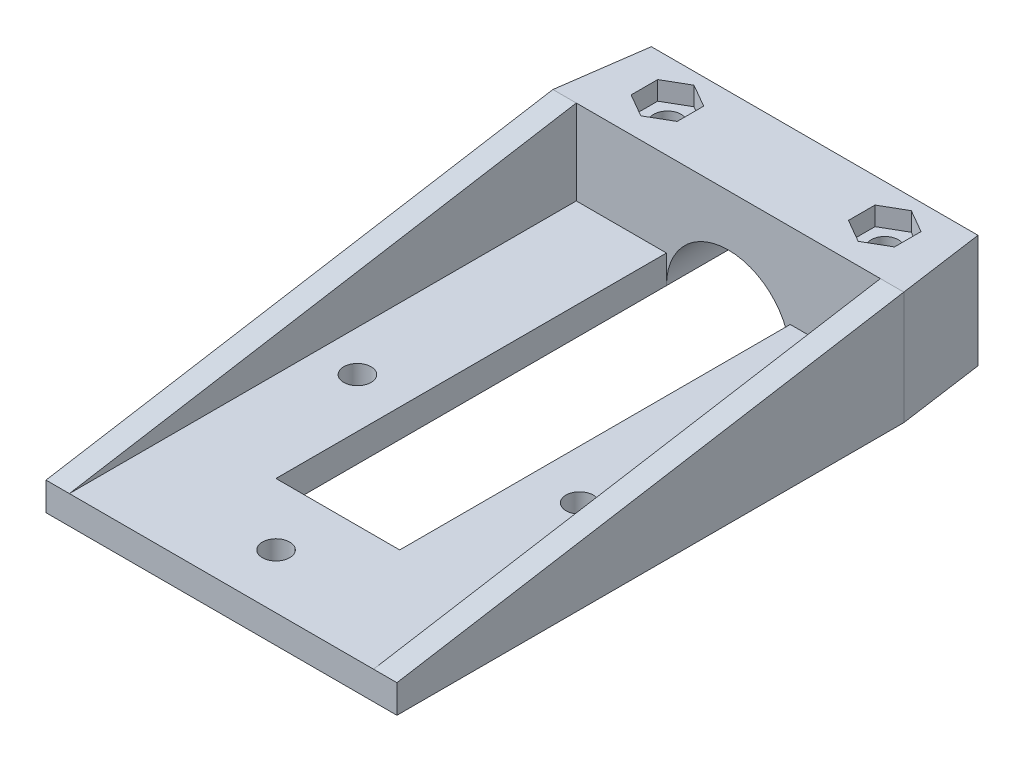
SolidWorks part; units mm, degrees
ref_plane "Front Plane" through (0, 0, 0) normal (0, 0, 1) x (1, 0, 0)
ref_plane "Top Plane" through (0, 0, 0) normal (0, 1, 0) x (1, 0, 0)
ref_plane "Right Plane" through (0, 0, 0) normal (1, 0, 0) x (0, 0, -1)
sketch "Sketch6" plane through (0, 0, 0) normal (0, 1, 0) x (1, 0, 0)
  line L0 (-16.8369, 5.7834) -> (13.1631, 5.7834)
  line L1 (13.1631, 5.7834) -> (20.6631, -47.5819)
  line L2 (20.6631, -47.5819) -> (-24.3369, -47.5819)
  line L3 (-24.3369, -47.5819) -> (-16.8369, 5.7834)
  circle A0 centre (13.1631, -5.2166) radius 1.78
  circle A1 centre (-16.8369, -5.2166) radius 1.78
  circle A2 centre (-26.4869, -43.0491) radius 1.78
  circle A3 centre (22.8131, -43.0491) radius 1.78
  dimension "D3" = 98
  dimension "D4" = 3.56
  dimension "D5" = 3.56
  dimension "D2" = 45
  dimension "D6" = 30
  dimension "D7" = 11
  dimension "D8" = 11
  dimension "D9" = 98
  dimension "D10" = 82
  dimension "D11" = 82
  dimension "D12" = 30
extrude "Boss-Extrude3" add sketch "Sketch6" along normal blind 14.5 contours L3 L0 L1 L2
sketch "Sketch8" plane through (0, 0, 47.5819) normal (0, 0, 1) x (1, 0, 0)
  line L0 (20.6631, 0) -> (-24.3369, 0) construction
  circle A0 centre (-1.8369, 0) radius 7.935
  dimension "D1" = 15.87
extrude "Cut-Extrude3" cut sketch "Sketch8" against normal blind 88
sketch "Sketch18" plane through (0, 14.5, 0) normal (0, 1, 0) x (1, 0, 0)
  line L0 (20.6631, -47.5819) -> (-24.3369, -47.5819) construction
  line L1 (-24.3369, -47.5819) -> (-16.8369, 5.7834) construction
  line L2 (13.1631, 5.7834) -> (20.6631, -47.5819) construction
  line L10 (-15.7718, -44.8683) -> (-12.8218, -43.1651)
  line L11 (-12.8218, -43.1651) -> (-12.8218, -39.7587)
  line L12 (-12.8218, -39.7587) -> (-15.7718, -38.0556)
  line L13 (-15.7718, -38.0556) -> (-18.7218, -39.7587)
  line L14 (-18.7218, -39.7587) -> (-18.7218, -43.1651)
  line L15 (-18.7218, -43.1651) -> (-15.7718, -44.8683)
  line L16 (12.098, -44.8683) -> (15.048, -43.1651)
  line L17 (15.048, -43.1651) -> (15.048, -39.7587)
  line L18 (15.048, -39.7587) -> (12.098, -38.0556)
  line L19 (12.098, -38.0556) -> (9.148, -39.7587)
  line L20 (9.148, -39.7587) -> (9.148, -43.1651)
  line L21 (9.148, -43.1651) -> (12.098, -44.8683)
  line L22 (11.3893, -26.016) -> (14.3893, -24.284)
  line L23 (14.3893, -24.284) -> (14.3893, -20.8199)
  line L24 (14.3893, -20.8199) -> (11.3893, -19.0878)
  line L25 (11.3893, -19.0878) -> (8.3893, -20.8199)
  line L26 (8.3893, -20.8199) -> (8.3893, -24.284)
  line L27 (8.3893, -24.284) -> (11.3893, -26.016)
  line L28 (-15.0632, -26.016) -> (-12.0632, -24.284)
  line L29 (-12.0632, -24.284) -> (-12.0632, -20.8199)
  line L30 (-12.0632, -20.8199) -> (-15.0632, -19.0878)
  line L31 (-15.0632, -19.0878) -> (-18.0632, -20.8199)
  line L32 (-18.0632, -20.8199) -> (-18.0632, -24.284)
  line L33 (-18.0632, -24.284) -> (-15.0632, -26.016)
  circle A0 centre (-15.0632, -22.5519) radius 3 construction
  circle A1 centre (-15.7718, -41.4619) radius 2.95 construction
  circle A2 centre (12.098, -41.4619) radius 2.95 construction
  circle A3 centre (11.3893, -22.5519) radius 3 construction
  point P0 (-15.7718, -41.4619)
  point P1 (-15.0632, -22.5519)
  point P2 (12.098, -41.4619)
  point P3 (11.3893, -22.5519)
  dimension "D1" = 6.12
  dimension "D2" = 7.63
  dimension "D3" = 25.03
  dimension "D4" = 5.7
  dimension "D5" = 6.12
  dimension "D6" = 7.63
  dimension "D7" = 25.03
  dimension "D8" = 5.7
  dimension "D9" = 6
  dimension "D10" = 5.9
  dimension "D11" = 5.9
  dimension "D12" = 6
sketch "Sketch19" plane through (0, 0, 0) normal (0, -1, 0) x (1, 0, 0)
  line L1 (-20.0152, 40.7177) -> (-17.249, 37.4149)
  line L2 (-17.249, 37.4149) -> (-13.0056, 38.1592)
  line L3 (-13.0056, 38.1592) -> (-11.5284, 42.2062)
  line L4 (-11.5284, 42.2062) -> (-14.2947, 45.5089)
  line L5 (-14.2947, 45.5089) -> (-18.5381, 44.7647)
  line L6 (-18.5381, 44.7647) -> (-20.0152, 40.7177)
  line L7 (-16.9187, 22.0232) -> (-15.5331, 20.6806)
  line L8 (-15.5331, 20.6806) -> (-13.6775, 21.2093)
  line L9 (-13.6775, 21.2093) -> (-13.2076, 23.0806)
  line L10 (-13.2076, 23.0806) -> (-14.5932, 24.4232)
  line L11 (-14.5932, 24.4232) -> (-16.4488, 23.8945)
  line L12 (-16.4488, 23.8945) -> (-16.9187, 22.0232)
  line L13 (16.8606, 20.993) -> (15.475, 26.5108)
  line L14 (15.475, 26.5108) -> (10.0037, 28.0696)
  line L15 (10.0037, 28.0696) -> (5.918, 24.1108)
  line L16 (5.918, 24.1108) -> (7.3037, 18.5931)
  line L17 (7.3037, 18.5931) -> (12.775, 17.0342)
  line L18 (12.775, 17.0342) -> (16.8606, 20.993)
  line L19 (20.0445, 40.0682) -> (17.2783, 47.6469)
  line L20 (17.2783, 47.6469) -> (9.3318, 49.0407)
  line L21 (9.3318, 49.0407) -> (4.1515, 42.8557)
  line L22 (4.1515, 42.8557) -> (6.9177, 35.2769)
  line L23 (6.9177, 35.2769) -> (14.8642, 33.8832)
  line L24 (14.8642, 33.8832) -> (20.0445, 40.0682)
  circle A0 centre (-15.7718, 41.4619) radius 3.731 construction
  circle A1 centre (-15.0632, 22.5519) radius 1.6709 construction
  circle A2 centre (11.3893, 22.5519) radius 4.9269 construction
  circle A3 centre (12.098, 41.4619) radius 6.9869 construction
  point P0 (-15.7718, 41.4619)
  point P1 (-15.0632, 22.5519)
  point P3 (11.3893, 22.5519)
  point P5 (12.098, 41.4619)
extrude "Cut-Extrude9" cut sketch "Sketch18" against normal blind 2.4
hole_wizard "#39 (0.13779528) Diameter Hole1" positions "3DSketch1" profile "Sketch21" hole size "#39" standard "ANSI Inch" end condition through all
sketch3d "3DSketch1"
  point P0 (-15.0632, 14.5, 22.5519)
  point P3 (11.3893, 14.5, 22.5519)
  point P6 (-15.7718, 14.5, 41.4619)
  point P9 (12.098, 14.5, 41.4619)
sketch "Sketch21" plane through (-15.0632, 14.5, 22.5519) normal (1, 0, 0) x (0, 0, 1)
  line L0 (0, 0) -> (0, 14.5)
  line L1 (0, 14.5) -> (1.75, 14.5)
  line L2 (1.75, 14.5) -> (1.75, 0)
  line L5 (1.75, 0) -> (0, 0)
  line L11 (0, -6.35) -> (0, 107.95) construction
  dimension "Thru Hole Dia." = 3.5
  dimension "Thru Hole Depth" = 14.5
sketch "Sketch22" plane through (0, 14.5, 0) normal (0, 1, 0) x (1, 0, 0)
  line L0 (-22.7813, -36.5132) -> (19.1075, -36.5132)
  line L1 (-24.3369, -47.5819) -> (-16.8369, 5.7834) construction
  line L2 (13.1631, 5.7834) -> (20.6631, -47.5819) construction
  line L3 (19.1075, -36.5132) -> (13.1631, 5.7834)
  line L4 (13.1631, 5.7834) -> (-16.8369, 5.7834)
  line L5 (-16.8369, 5.7834) -> (-22.7813, -36.5132)
extrude "Cut-Extrude10" cut sketch "Sketch22" against normal blind 22.4
sketch "Sketch23" plane through (0, 0, 47.5819) normal (0, 0, 1) x (1, 0, 0)
  line L0 (-24.3369, 0) -> (-24.3369, 3.625)
  line L1 (-24.3369, 14.5) -> (-24.3369, 0) construction
  line L2 (-24.3369, 3.625) -> (-8.8955, 3.625)
  line L3 (20.6631, 0) -> (20.6631, 3.625)
  line L4 (20.6631, 14.5) -> (20.6631, 0) construction
  line L5 (20.6631, 3.625) -> (5.2217, 3.625)
  line L6 (-24.3369, 0) -> (-9.7719, 0)
  line L7 (20.6631, 0) -> (6.0981, 0) construction
  arc A0 (6.0981, 0) -> (-9.7719, 0) centre (-1.8369, 0) ccw construction
  spline S0 degree 2 poles (-9.7719, 0) (-9.7646, 1.9214) (-8.8955, 3.625) knots 0 0 0 1 1 1
  spline S1 degree 2 poles (6.0981, 0) (6.0907, 1.9214) (5.2217, 3.625) knots 0 0 0 1 1 1
  dimension "D1" = 3.625
  dimension "D2" = 3.625
sketch "Sketch24" plane through (0, 0, 0) normal (0, -1, 0) x (1, 0, 0)
  line L1 (-15.7718, 38.0556) -> (-12.8218, 39.7587)
  line L2 (-12.8218, 39.7587) -> (-12.8218, 43.1651)
  line L3 (-12.8218, 43.1651) -> (-15.7718, 44.8683)
  line L4 (-15.7718, 44.8683) -> (-18.7218, 43.1651)
  line L5 (-18.7218, 43.1651) -> (-18.7218, 39.7587)
  line L6 (-18.7218, 39.7587) -> (-15.7718, 38.0556)
  line L7 (12.098, 38.0556) -> (15.048, 39.7587)
  line L8 (15.048, 39.7587) -> (15.048, 43.1651)
  line L9 (15.048, 43.1651) -> (12.098, 44.8683)
  line L10 (12.098, 44.8683) -> (9.148, 43.1651)
  line L11 (9.148, 43.1651) -> (9.148, 39.7587)
  line L12 (9.148, 39.7587) -> (12.098, 38.0556)
  circle A0 centre (-15.7718, 41.4619) radius 2.95 construction
  circle A1 centre (12.098, 41.4619) radius 2.95 construction
  point P0 (-15.7718, 41.4619)
  point P1 (12.098, 41.4619)
  dimension "D1" = 5.9
  dimension "D2" = 5.9
extrude "Cut-Extrude11" cut sketch "Sketch24" against normal blind 2.4
sketch "Sketch27" plane through (0, 0, 0) normal (0, 1, 0) x (1, 0, 0)
  line L0 (-9.7719, -47.2249) -> (-9.7719, -47.5819)
  line L1 (-9.7719, -47.5819) -> (-9.7719, -97.6619)
  line L2 (-9.7719, -112.5819) -> (-24.3369, -112.5819)
  line L3 (-24.3369, -112.5819) -> (-24.3369, -47.5819)
  line L4 (-9.7719, -97.6619) -> (6.0981, -97.6619)
  line L5 (6.0981, -47.5819) -> (6.0981, -97.6619)
  line L6 (20.6631, -47.5819) -> (20.6631, -112.5819)
  line L7 (20.6631, -112.5819) -> (-9.7719, -112.5819)
  line L9 (-24.3369, -47.5819) -> (-9.7719, -47.5819)
  line L10 (-24.3369, -47.5819) -> (-9.7719, -47.5819)
  line L11 (6.0981, -47.5819) -> (20.6631, -47.5819)
  dimension "D1" = 65
  dimension "D2" = 14.92
  dimension "D3" = 15.87
extrude "Boss-Extrude7" add sketch "Sketch27" along normal up to vertex (3.625 mm away) contours L11 L5 L4 L1 L9 L3 L2 L7 L6 up to point (20.6631, 3.625, 47.5819)
sketch "Sketch30" plane through (0, 3.625, 0) normal (0, 1, 0) x (1, 0, 0)
  line L0 (20.6631, -112.5819) -> (-24.3369, -112.5819) construction
  line L2 (20.6631, -47.5819) -> (20.6631, -112.5819) construction
  line L3 (-16.0869, -80.9002) -> (-1.8369, -105.5819)
  line L4 (-1.8369, -105.5819) -> (12.4131, -80.9002)
  line L5 (12.4131, -80.9002) -> (-16.0869, -80.9002)
  line L6 (6.0981, -47.5819) -> (6.0981, -97.6619) construction
  line L7 (-9.7719, -47.5819) -> (-9.7719, -97.6619) construction
  point P0 (-16.0869, -80.9002)
  point P1 (12.4131, -80.9002)
  point P2 (-1.8369, -105.5819)
  dimension "D2" = 28.5
  dimension "D3" = 28.5
  dimension "D4" = 60
  dimension "D5" = 60
  dimension "D6" = 22.5
  dimension "D7" = 60
  dimension "D8" = 6.315
  dimension "D9" = 6.315
  dimension "D10" = 7
  dimension "D11" = 28.5
hole_wizard "#39 (0.13779528) Diameter Hole2" positions "3DSketch2" profile "Sketch31" hole size "#39" standard "ANSI Inch" end condition through all
sketch3d "3DSketch2"
  point P0 (-16.0869, 3.625, 80.9002)
  point P3 (-1.8369, 3.625, 105.5819)
  point P6 (12.4131, 3.625, 80.9002)
sketch "Sketch31" plane through (-16.0869, 3.625, 80.9002) normal (1, 0, 0) x (0, 0, 1)
  line L0 (0, 0) -> (0, 3.625)
  line L1 (0, 3.625) -> (1.75, 3.625)
  line L2 (1.75, 3.625) -> (1.75, 0)
  line L5 (1.75, 0) -> (0, 0)
  line L11 (0, -6.35) -> (0, 107.95) construction
  dimension "Thru Hole Dia." = 3.5
  dimension "Thru Hole Depth" = 3.625
sketch "Sketch39" plane through (20.6631, 0, 0) normal (1, 0, 0) x (0, 0, -1)
  line L0 (-47.5819, 14.5) -> (-112.5819, 3.625)
  line L1 (-112.5819, 3.625) -> (-47.5819, 3.625)
  line L2 (-47.5819, 3.625) -> (-47.5819, 14.5)
extrude "Boss-Extrude10" add sketch "Sketch39" against normal blind 3
sketch "Sketch40" plane through (-24.3369, 0, 0) normal (-1, 0, 0) x (0, 0, 1)
  line L0 (47.5819, 14.5) -> (112.5819, 3.625)
  line L1 (112.5819, 3.625) -> (47.5819, 3.625)
  line L2 (47.5819, 3.625) -> (47.5819, 14.5)
extrude "Boss-Extrude11" add sketch "Sketch40" against normal blind 3
